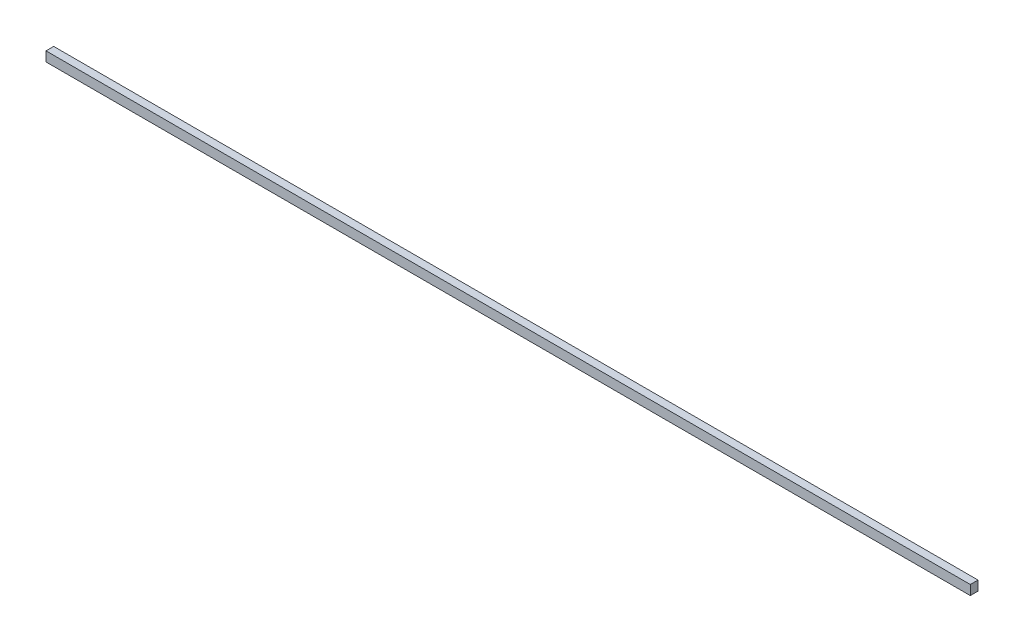
SolidWorks part; units mm, degrees
ref_plane "Front Plane" through (0, 0, 0) normal (0, 0, 1) x (1, 0, 0)
ref_plane "Top Plane" through (0, 0, 0) normal (0, 1, 0) x (1, 0, 0)
ref_plane "Right Plane" through (0, 0, 0) normal (1, 0, 0) x (0, 0, -1)
sketch "Sketch1" plane through (0, 0, 0) normal (0, 0, 1) x (1, 0, 0)
  line L1 (-304.8, -3.175) -> (304.8, -3.175)
  line L2 (-304.8, -3.175) -> (-304.8, 3.175)
  line L3 (-304.8, 3.175) -> (304.8, 3.175)
  line L4 (304.8, -3.175) -> (304.8, 3.175)
  line L5 (-304.8, -3.175) -> (304.8, 3.175) construction
  line L6 (-304.8, 3.175) -> (304.8, -3.175) construction
  point P0 (0, 0)
  dimension "D1" = 609.6
  dimension "D2" = 6.35
extrude "Boss-Extrude1" add sketch "Sketch1" along normal mid plane 5.08
